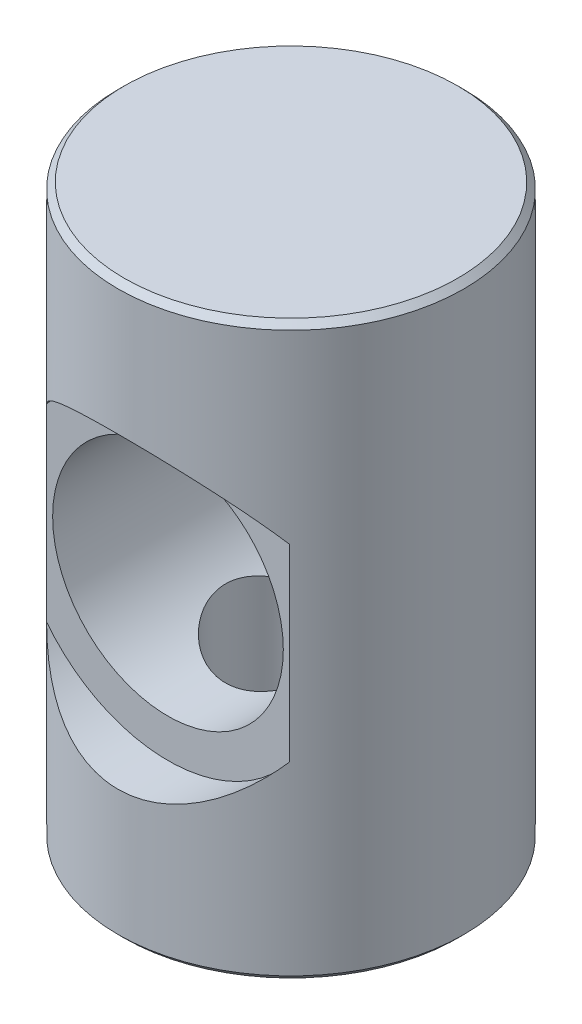
SolidWorks part; units mm, degrees
ref_plane "Front Plane" through (0, 0, 0) normal (0, 0, 1) x (1, 0, 0)
ref_plane "Top Plane" through (0, 0, 0) normal (0, 1, 0) x (1, 0, 0)
ref_plane "Right Plane" through (0, 0, 0) normal (1, 0, 0) x (0, 0, -1)
sketch "Sketch1" plane through (0, 0, 0) normal (0, 1, 0) x (1, 0, 0)
  circle A0 centre (0, 0) radius 7.1374
  dimension "D1" = 14.2748
extrude "Boss-Extrude1" add sketch "Sketch1" along normal blind 23.5966
chamfer "Chamfer1" distance 0.254 angle 45 1 edges at (0, 0, 7.1374)
chamfer "Chamfer2" distance 0.254 angle 45 1 edges at (0, 23.5966, 7.1374)
sketch "Sketch2" plane through (0, 0, 0) normal (0, 0, 1) x (1, 0, 0)
  line L0 (0, 0) -> (0, 23.5966) construction
  line L1 (6.8834, 23.5966) -> (-6.8834, 23.5966) construction
  circle A1 centre (0, 11.7983) radius 4.7625
  dimension "D1" = 9.525
extrude "Cut-Extrude1" cut sketch "Sketch2" against normal mid plane 14.351 contours A1
ref_plane "Plane1" through (0, 0, 5.08) normal (0, 0, 1) x (1, 0, 0)
sketch "Sketch3" plane through (0, 0, 5.08) normal (0, 0, 1) x (1, 0, 0)
  circle A0 centre (0, 11.7983) radius 6.35
  dimension "D1" = 12.7
extrude "Cut-Extrude2" cut sketch "Sketch3" along normal through all
mirror "Mirror1" about plane through (0, 0, 0) normal (0, 0, 1) of "Cut-Extrude2"
hole_wizard "1/4-28 Tapped Hole1" positions "Sketch4" profile "Sketch5" tap size "1/4-28" standard "ANSI Inch"
sketch "Sketch4" plane through (0, 0, 0) normal (0, -1, 0) x (-1, 0, 0)
  circle A0 centre (0, 0) radius 6.8834 construction
  point P0 (0, 0)
sketch "Sketch5" plane through (0, 0, 0) normal (1, 0, 0) x (0, 0, -1)
  line L0 (0, 0) -> (0, 7.0358)
  line L1 (0, 7.0358) -> (2.7051, 7.0358)
  line L2 (2.7051, 7.0358) -> (2.7051, 0)
  line L5 (2.7051, 0) -> (0, 0)
  line L11 (0, -6.35) -> (0, 107.95) construction
  dimension "Thru Tap Drill Dia." = 5.4102
  dimension "Thru Tap Drill Depth" = 7.0358
cosmetic thread "Hole Thread1" parameters "D2"=6.35
